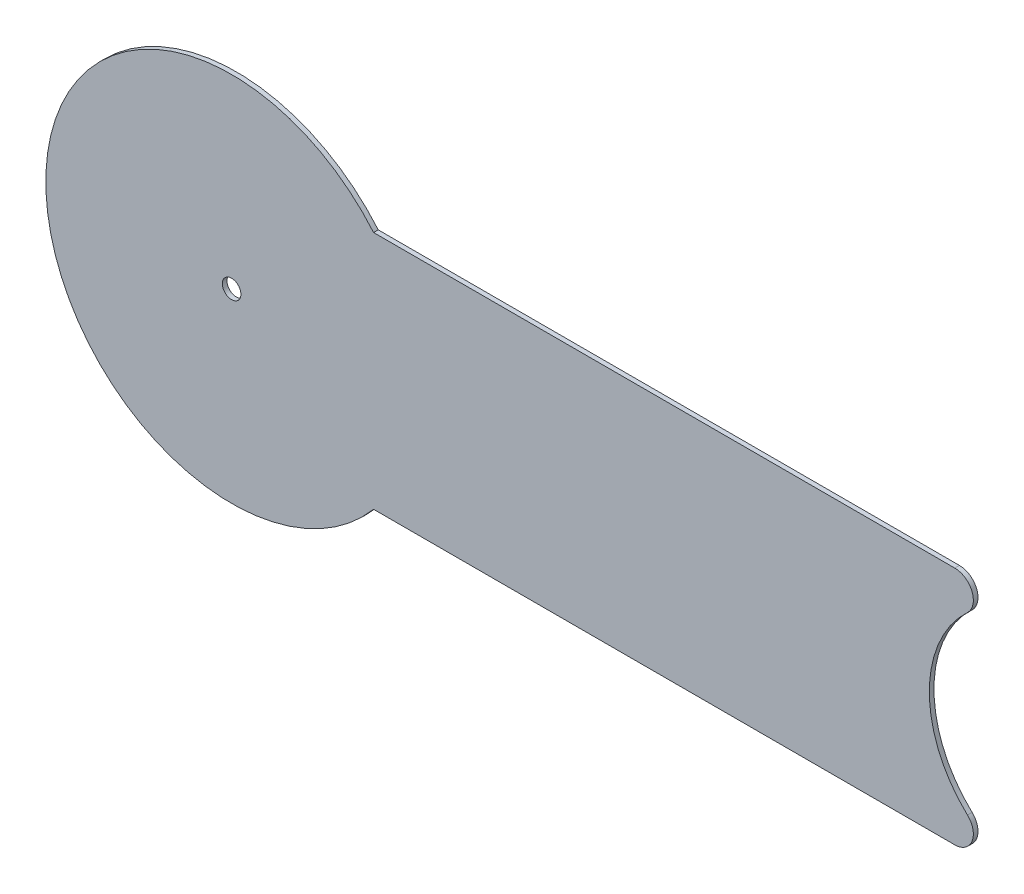
SolidWorks part; units mm, degrees
ref_plane "Front Plane" through (0, 0, 0) normal (0, 0, 1) x (1, 0, 0)
ref_plane "Top Plane" through (0, 0, 0) normal (0, 1, 0) x (1, 0, 0)
ref_plane "Right Plane" through (0, 0, 0) normal (1, 0, 0) x (0, 0, -1)
sketch "Sketch1" plane through (0, 0, 0) normal (0, 0, 1) x (1, 0, 0)
  line L0 (0, 0) -> (279.4, 0) construction
  line L1 (279.4, 42.545) -> (51.3369, 42.545) construction
  line L2 (51.3369, -42.545) -> (279.4, -42.545) construction
  line L3 (247.146, -40.9575) -> (48.5256, -40.9575)
  line L4 (247.146, 40.9575) -> (48.5256, 40.9575)
  arc A0 (51.3369, 42.545) -> (51.3369, -42.545) centre (0, 0) ccw construction
  arc A1 (279.4, -42.545) -> (279.4, 42.545) centre (279.4, 0) ccw construction
  arc A2 (48.5256, 40.9575) -> (48.5256, -40.9575) centre (0, 0) ccw
  arc A3 (247.146, -40.9575) -> (251.4754, -29.9622) centre (247.146, -34.6075) ccw
  circle A4 centre (0, 0) radius 3.175
  arc A5 (247.146, 40.9575) -> (251.4754, 29.9622) centre (247.146, 34.6075) cw
  arc A7 (251.4754, 29.9622) -> (251.4754, -29.9622) centre (279.4, 0) ccw
  point P6 (279.4, -40.9575)
  point P17 (279.4, 40.9575)
  dimension "D1" = 127
  dimension "D2" = 3.175
  dimension "D3" = 3.175
  dimension "D4" = 42.545
  dimension "D6" = 6.35
  dimension "D7" = 6.35
  dimension "D5" = 279.4
extrude "Boss-Extrude1" add sketch "Sketch1" along normal blind 1.5875
equation "\"D4@Sketch1\"=3.35/2"
